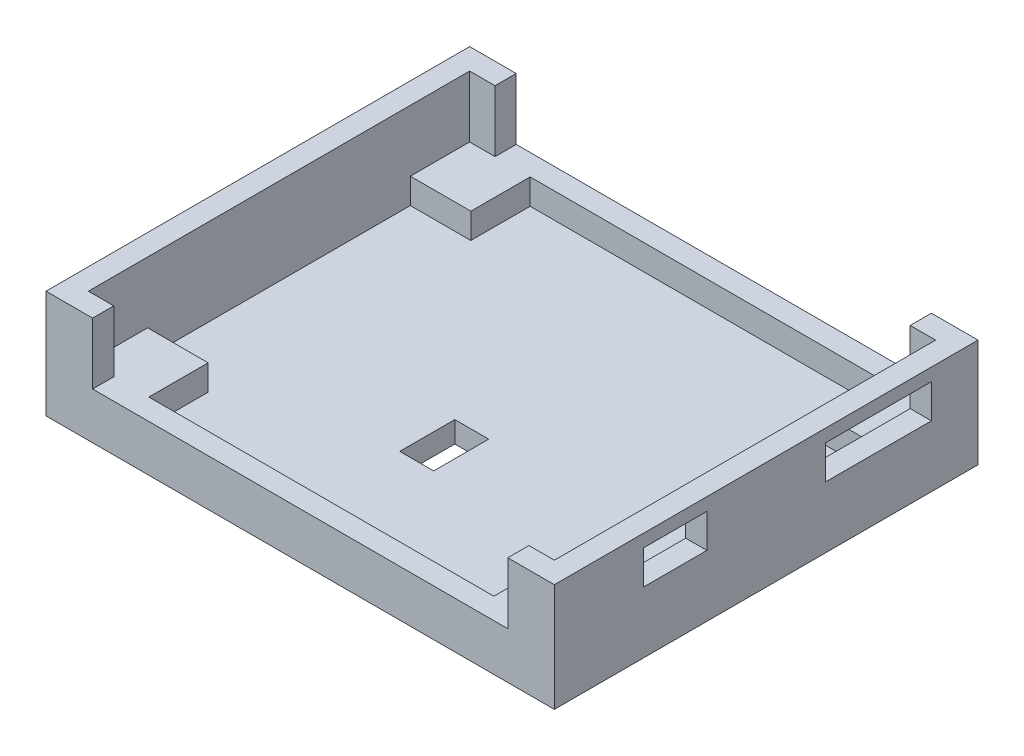
SolidWorks part; units mm, degrees
ref_plane "Front Plane" through (0, 0, 0) normal (0, 0, 1) x (1, 0, 0)
ref_plane "Top Plane" through (0, 0, 0) normal (0, 1, 0) x (1, 0, 0)
ref_plane "Right Plane" through (0, 0, 0) normal (1, 0, 0) x (0, 0, -1)
sketch "Croquis1" plane through (0, 0, 0) normal (0, 1, 0) x (1, 0, 0)
  line L1 (-30, 25) -> (30, 25)
  line L2 (-30, 25) -> (-30, -25)
  line L3 (-30, -25) -> (30, -25)
  line L4 (30, 25) -> (30, -25)
  line L5 (-30, 25) -> (30, -25) construction
  line L6 (-30, -25) -> (30, 25) construction
  point P0 (0, 0)
  dimension "D1" = 60
  dimension "D2" = 50
extrude "Saliente-Extruir1" add sketch "Croquis1" along normal blind 12.75
sketch "Croquis2" plane through (0, 0, 0) normal (0, 1, 0) x (1, 0, 0)
  line L0 (30, 25) -> (-30, 25) construction
  line L1 (-27.5, 22.5) -> (27.5, 22.5)
  line L2 (-27.5, 22.5) -> (-27.5, -22.5)
  line L3 (-27.5, -22.5) -> (27.5, -22.5)
  line L4 (27.5, 22.5) -> (27.5, -22.5)
  line L5 (-27.5, 22.5) -> (27.5, -22.5) construction
  line L6 (-27.5, -22.5) -> (27.5, 22.5) construction
  line L7 (-30, 25) -> (-30, -25) construction
  point P0 (0, 0)
  dimension "D1" = 2.5
  dimension "D2" = 2.5
extrude "Cortar-Extruir2" cut sketch "Croquis2" against normal blind 10.25 from surface at 12.75 starting at face at (0, 12.75, 0)
sketch "Croquis3" plane through (0, 0, 0) normal (0, 1, 0) x (1, 0, 0)
  line L0 (-27.5, -22.5) -> (-27.5, 22.5) construction
  line L1 (-3, -3.75) -> (1, -3.75)
  line L2 (-3, -3.75) -> (-3, -10.25)
  line L3 (-3, -10.25) -> (1, -10.25)
  line L4 (1, -3.75) -> (1, -10.25)
  line L5 (-3, -3.75) -> (1, -10.25) construction
  line L6 (-3, -10.25) -> (1, -3.75) construction
  line L8 (27.5, -22.5) -> (-27.5, -22.5) construction
  point P0 (-1, -7)
  dimension "D1" = 4
  dimension "D2" = 6.5
  dimension "D3" = 28.5
  dimension "D4" = 18.75
extrude "Cortar-Extruir3" cut sketch "Croquis3" along normal blind 10.25
sketch "Croquis5" plane through (0, 0, 0) normal (0, 0, 1) x (1, 0, 0)
  line L0 (-30, 12.75) -> (-24.5, 12.75) construction
  line L1 (-30, 12.75) -> (30, 12.75) construction
  line L2 (0, 0) -> (0, 12.75) construction
  line L3 (30, 12.75) -> (24.5, 12.75) construction
  line L4 (-24.5, 5.5) -> (24.5, 5.5)
  line L5 (-30, 0) -> (30, 0) construction
  line L6 (-24.5, 12.75) -> (-24.5, 5.5)
  line L7 (24.5, 12.75) -> (24.5, 5.5)
  line L8 (-24.5, 12.75) -> (24.5, 12.75)
  dimension "D1" = 5.5
  dimension "D2" = 5.5
extrude "Cortar-Extruir4" cut sketch "Croquis5" against normal mid plane 90.25
sketch "Croquis6" plane through (0, 0, 0) normal (1, 0, 0) x (0, 0, -1)
  line L0 (-25, 0) -> (25, 0) construction
  line L1 (-14.5, 11.25) -> (-7, 11.25)
  line L2 (-14.5, 11.25) -> (-14.5, 7.25)
  line L3 (-14.5, 7.25) -> (-7, 7.25)
  line L4 (-7, 11.25) -> (-7, 7.25)
  line L5 (-14.5, 11.25) -> (-7, 7.25) construction
  line L6 (-14.5, 7.25) -> (-7, 11.25) construction
  line L7 (-22.5, 2.5) -> (-22.5, 12.75) construction
  line L8 (-12.8375, 6.25) -> (-8.487, 6.25) construction
  line L9 (7, 11.25) -> (19.5, 11.25)
  line L10 (7, 11.25) -> (7, 7.25)
  line L11 (7, 7.25) -> (19.5, 7.25)
  line L12 (19.5, 11.25) -> (19.5, 7.25)
  line L13 (7, 11.25) -> (19.5, 7.25) construction
  line L14 (7, 7.25) -> (19.5, 11.25) construction
  point P0 (-10.75, 9.25)
  point P9 (13.25, 9.25)
  dimension "D1" = 11.25
  dimension "D2" = 4
  dimension "D3" = 7.5
  dimension "D4" = 15.5
  dimension "D5" = 14
  dimension "D6" = 4
  dimension "D7" = 12.5
  dimension "D8" = 11.25
  dimension "D9" = 1
extrude "Cortar-Extruir5" cut sketch "Croquis6" along normal blind 60
sketch "Croquis8" plane through (0, 0, 0) normal (0, 1, 0) x (1, 0, 0)
  line L0 (27.5, -15.5) -> (20.3586, -15.5)
  line L1 (27.5, 22.5) -> (27.5, -22.5) construction
  line L2 (20.3586, -15.5) -> (20.3586, -22.5)
  line L3 (27.5, -22.5) -> (-27.5, -22.5) construction
  line L4 (20.3586, -22.5) -> (27.5, -22.5)
  line L5 (27.5, -22.5) -> (27.5, -15.5)
  line L6 (-24.5396, 0) -> (23.3802, 0) construction
  line L7 (0, 17.5513) -> (0, -17.4224) construction
  line L8 (-20.3586, -22.5) -> (-27.5, -22.5)
  line L9 (-27.5, -22.5) -> (-27.5, -15.5)
  line L10 (-27.5, -15.5) -> (-20.3586, -15.5)
  line L11 (-20.3586, -15.5) -> (-20.3586, -22.5)
  line L12 (20.3586, 22.5) -> (27.5, 22.5)
  line L13 (27.5, 22.5) -> (27.5, 15.5)
  line L14 (20.3586, 15.5) -> (20.3586, 22.5)
  line L15 (27.5, 15.5) -> (20.3586, 15.5)
  line L16 (-27.5, 22.5) -> (-27.5, 15.5)
  line L17 (-20.3586, 22.5) -> (-27.5, 22.5)
  line L18 (-20.3586, 15.5) -> (-20.3586, 22.5)
  line L19 (-27.5, 15.5) -> (-20.3586, 15.5)
  dimension "D1" = 10
  dimension "D2" = 7
extrude "Saliente-Extruir6" add sketch "Croquis8" along normal blind 5.5
